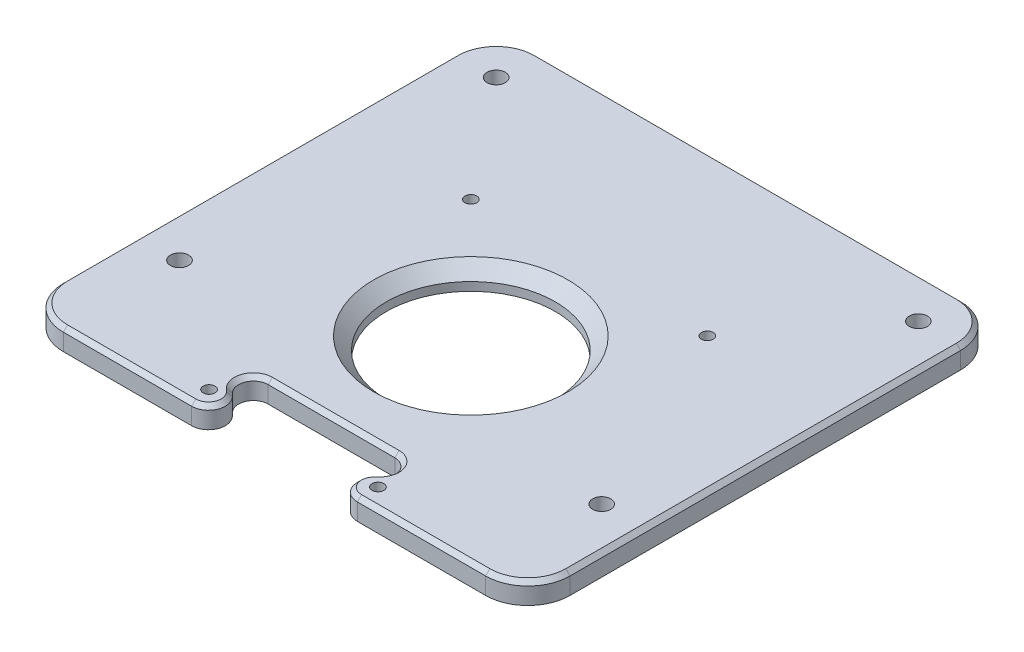
SolidWorks part; units mm, degrees
ref_plane "Front Plane" through (0, 0, 0) normal (0, 0, 1) x (1, 0, 0)
ref_plane "Top Plane" through (0, 0, 0) normal (0, 1, 0) x (1, 0, 0)
ref_plane "Right Plane" through (0, 0, 0) normal (1, 0, 0) x (0, 0, -1)
sketch "Sketch1" plane through (0, 0, 0) normal (0, 1, 0) x (1, 0, 0)
  line L0 (0, 0) -> (0, -28) construction
  line L1 (0, -28) -> (-28, -28) construction
  line L2 (0, -28) -> (28, -28) construction
  line L3 (0, 0) -> (0, 42) construction
  line L4 (0, 42) -> (20, 42) construction
  line L5 (0, 42) -> (-20, 42) construction
  line L6 (-15, -36.5) -> (15, -36.5) construction
  line L7 (-15, -34.85) -> (15, -34.85)
  line L8 (-15, -38.15) -> (15, -38.15)
  line L9 (0, 0) -> (0, -36.5) construction
  line L10 (-35, 0) -> (35, 0) construction
  circle A0 centre (0, 0) radius 35 construction
  arc A5 (-15, -34.85) -> (-15, -38.15) centre (-15, -36.5) ccw
  arc A6 (15, -38.15) -> (15, -34.85) centre (15, -36.5) ccw
  circle A7 centre (28, 28) radius 1.4
  circle A8 centre (-28, 28) radius 1.4
  circle A9 centre (20, -42) radius 1.4
  circle A10 centre (-20, -42) radius 1.4
  point P15 (0, -36.5)
  dimension "D1" = 70
  dimension "D9" = 1.65
  dimension "D2" = 28
  dimension "D3" = 42
  dimension "D4" = 56
  dimension "D5" = 40
  dimension "D7" = 30
  dimension "D8" = 36.5
sketch "Sketch2" plane through (0, 0, 0) normal (0, 1, 0) x (1, 0, 0)
  line L0 (0, 0) -> (0, 66) construction
  line L1 (-60, 66) -> (60, 66)
  line L2 (-60, 66) -> (-60, -46.5)
  line L4 (60, 66) -> (60, -46.5)
  line L6 (-60, -46.5) -> (60, -46.5)
  point P5 (0, 0)
  dimension "D1" = 120
  dimension "D2" = 112.5
  dimension "D3" = 66
extrude "Boss-Extrude2" add sketch "Sketch2" along normal blind 5
sketch "Sketch9" plane through (0, 5, 0) normal (0, 1, 0) x (1, 0, 0)
  line L0 (-15, -36.5) -> (15, -36.5) construction
  line L1 (-15, -33) -> (15, -33) construction
  line L2 (-15, -40) -> (15, -40) construction
  line L3 (-17.4749, -34.0251) -> (-23.4497, -40)
  line L4 (-23.4497, -40) -> (23.4497, -40)
  line L5 (23.4497, -40) -> (17.4749, -34.0251)
  line L6 (-15, -33) -> (15, -33)
  line L7 (-23.4497, -40) -> (-29.9497, -46.5)
  line L8 (-60, -46.5) -> (60, -46.5) construction
  line L9 (23.4497, -40) -> (29.9497, -46.5)
  line L10 (29.9497, -46.5) -> (-29.9497, -46.5)
  line L11 (17.4777, -38.972) -> (10.1963, -46.5)
  line L12 (0, -33) -> (0, -46.5) construction
  line L14 (-17.4777, -38.972) -> (-10.1963, -46.5)
  arc A0 (-15, -33) -> (-15, -40) centre (-15, -36.5) ccw construction
  arc A1 (15, -40) -> (15, -33) centre (15, -36.5) ccw construction
  arc A2 (-17.4749, -34.0251) -> (-15, -33) centre (-15, -36.5) cw
  arc A3 (15, -33) -> (17.4749, -34.0251) centre (15, -36.5) cw
  arc A4 (-17.4749, -34.0251) -> (-18.5, -36.5) centre (-15, -36.5) ccw
  arc A5 (17.4749, -34.0251) -> (18.5, -36.5) centre (15, -36.5) cw
  arc A6 (-18.5, -36.5) -> (-17.4777, -38.972) centre (-15, -36.5) ccw
  arc A7 (18.5, -36.5) -> (17.4777, -38.972) centre (15, -36.5) cw
  point P2 (0, -36.5)
  point P29 (-17.8224, -38.5697)
  point P31 (-17.7144, -38.7095)
  point P32 (0, 0)
  point P33 (0, 0)
  point P34 (-11.3507, -46.5)
  point P35 (-10.0608, -46.5)
  point P36 (-17.4749, -38.972)
  point P37 (-10.1963, -46.5)
  dimension "D1" = 3.5
  dimension "D2" = 45
extrude "Cut-Extrude7" cut sketch "Sketch9" against normal through all contours A3 L6 A2 L3 L4 L5 | L4 L14 L10 L11
fillet "Fillet5" radius 10 4 edges at (-60, 2.5, -66) (60, 2.5, -66) (60, 2.5, 46.5) (-60, 2.5, 46.5)
sketch "Sketch10" plane through (0, 0, 0) normal (0, 1, 0) x (1, 0, 0)
  circle A0 centre (0, 0) radius 20
  dimension "D1" = 40
extrude "Cut-Extrude9" cut sketch "Sketch10" along normal through all
chamfer "Chamfer3" distance 3 angle 45 1 edges at (0, 5, 20)
fillet "Fillet6" radius 4 2 edges at (-10.1963, 2.5, 46.5) (10.1963, 2.5, 46.5)
chamfer "Chamfer4" distance 1 angle 45 16 edges at (-18.2328, 5, 35.1587) (0, 5, 33) (-34.8151, 5, 46.5) (18.2328, 5, 35.1587) (-57.0711, 5, 43.5711) (-60, 5, -9.75) (-57.0711, 5, -63.0711) (34.8151, 5, 46.5) (0, 5, -66) (57.0711, 5, 43.5711) (57.0711, 5, -63.0711) (60, 5, -9.75) (-17.1164, 5, 39.3455) (-15.9476, 5, 44.0614) (17.1164, 5, 39.3455) (15.9476, 5, 44.0614)
sketch "Sketch11" plane through (0, 5, 0) normal (0, 1, 0) x (1, 0, 0)
  line L0 (0, 0) -> (0, 42) construction
  line L1 (50, -19) -> (-50, -19) construction
  line L2 (50, -19) -> (50, 56) construction
  line L3 (50, 56) -> (-50, 56) construction
  line L4 (-50, -19) -> (-50, 56) construction
  line L5 (50, -19) -> (-50, 56) construction
  line L6 (50, 56) -> (-50, -19) construction
  circle A0 centre (-50, 56) radius 2.15
  circle A1 centre (50, 56) radius 2.15
  circle A2 centre (-50, -19) radius 2.15
  circle A3 centre (50, -19) radius 2.15
  point P0 (0, 18.5)
  dimension "D4" = 4.3
  dimension "D1" = 100
  dimension "D2" = 56
  dimension "D3" = 75
extrude "Cut-Extrude10" cut sketch "Sketch11" against normal through all
extrude "Cut-Extrude13" cut sketch "Sketch1" along normal up to surface (5 mm away) contours A10 | A9 | A7 | A8 up to face at (50, 5, -53.85)
sketch "Sketch13" plane through (0, 0, 0) normal (0, -1, 0) x (1, 0, 0)
  circle A0 centre (-20, 42) radius 2.875
  circle A1 centre (20, 42) radius 2.875
  circle A2 centre (-28, -28) radius 2.875
  circle A3 centre (28, -28) radius 2.875
  point P12 (0, 0)
  point P14 (0, 0)
  point P15 (0, 0)
  point P16 (0, 0)
  point P17 (0, 0)
  point P18 (0, 0)
  point P20 (0, 0)
  point P22 (0, 0)
  dimension "D1" = 5.75
extrude "Cut-Extrude12" cut sketch "Sketch13" against normal blind 2.5
